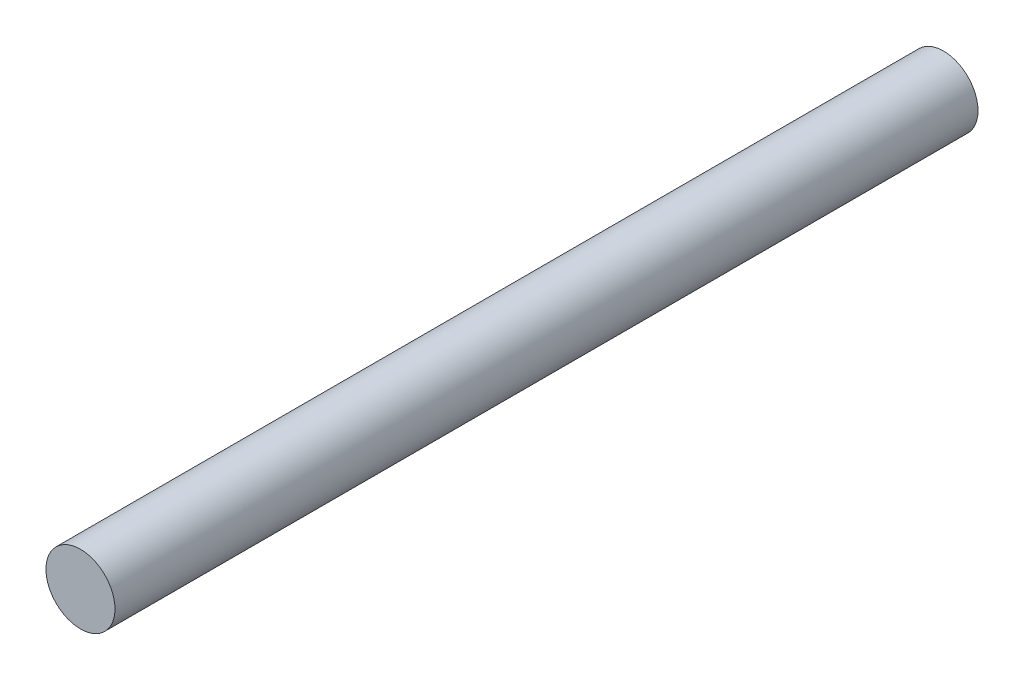
SolidWorks part; units mm, degrees
ref_plane "Plan de face" through (0, 0, 0) normal (0, 0, 1) x (1, 0, 0)
ref_plane "Plan de dessus" through (0, 0, 0) normal (0, 1, 0) x (1, 0, 0)
ref_plane "Plan de droite" through (0, 0, 0) normal (1, 0, 0) x (0, 0, -1)
sketch "Esquisse1" plane through (0, 0, 0) normal (0, 0, 1) x (1, 0, 0)
  circle A0 centre (0, 0) radius 4
  dimension "D1" = 8
extrude "Boss.-Extru.1" add sketch "Esquisse1" along normal blind 100
